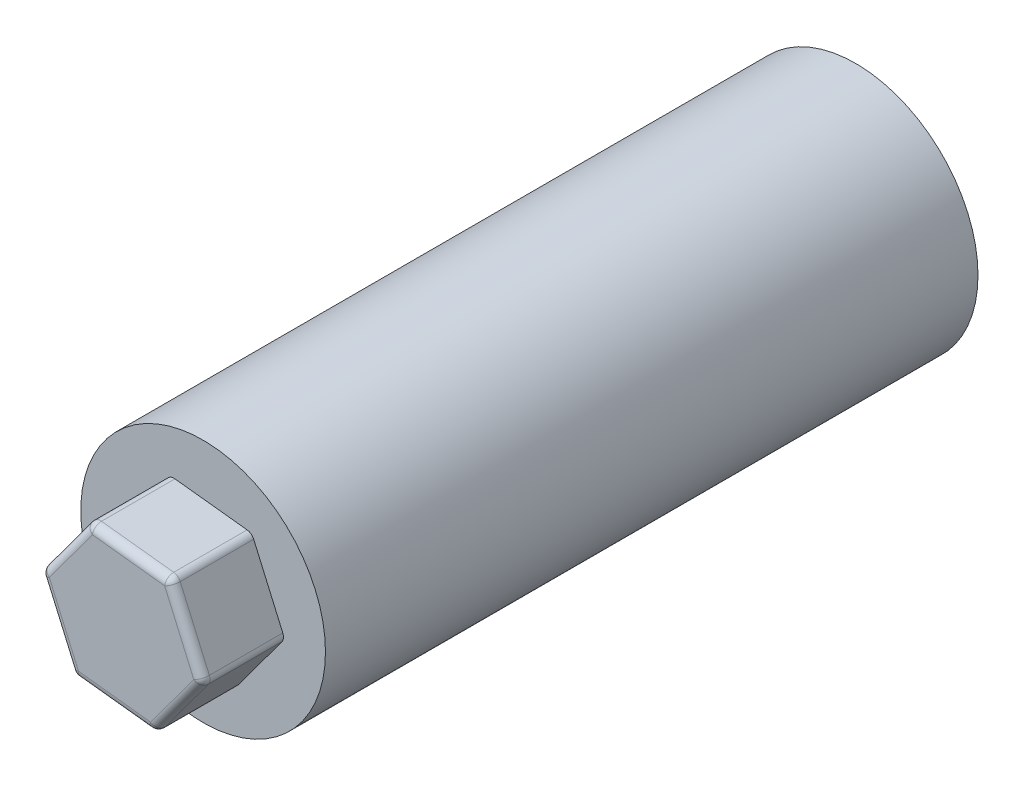
SolidWorks part; units mm, degrees
ref_plane "Front Plane" through (0, 0, 0) normal (0, 0, 1) x (1, 0, 0)
ref_plane "Top Plane" through (0, 0, 0) normal (0, 1, 0) x (1, 0, 0)
ref_plane "Right Plane" through (0, 0, 0) normal (1, 0, 0) x (0, 0, -1)
sketch "Sketch1" plane through (0, 0, 0) normal (0, 0, 1) x (1, 0, 0)
  circle A0 centre (0, 0) radius 15
  dimension "D1" = 30
extrude "Boss-Extrude1" add sketch "Sketch1" along normal blind 80
sketch "Sketch2" plane through (0, 0, 0) normal (0, 0, -1) x (-1, 0, 0)
  circle A0 centre (0, 0) radius 4
  dimension "D1" = 8
extrude "Cut-Extrude1" cut sketch "Sketch2" against normal blind 15
sketch "Sketch4" plane through (0, 0, 80) normal (0, 0, 1) x (1, 0, 0)
  line L1 (5.9697, 8.1004) -> (-4.0303, 9.2201)
  line L2 (-4.0303, 9.2201) -> (-10, 1.1198)
  line L3 (-10, 1.1198) -> (-5.9697, -8.1004)
  line L4 (-5.9697, -8.1004) -> (4.0303, -9.2201)
  line L5 (4.0303, -9.2201) -> (10, -1.1198)
  line L6 (10, -1.1198) -> (5.9697, 8.1004)
  circle A0 centre (0, 0) radius 8.7144 construction
  dimension "D1" = 10
extrude "Boss-Extrude2" add sketch "Sketch4" along normal blind 10
fillet "Fillet1" radius 1 12 edges at (4.0303, -9.2201, 85) (7.0151, -5.17, 90) (10, -1.1198, 85) (-10, 1.1198, 85) (-5.9697, -8.1004, 85) (-0.9697, -8.6603, 90) (-7.9849, -3.4903, 90) (-7.0151, 5.17, 90) (0.9697, 8.6603, 90) (7.9849, 3.4903, 90) (5.9697, 8.1004, 85) (-4.0303, 9.2201, 85)
